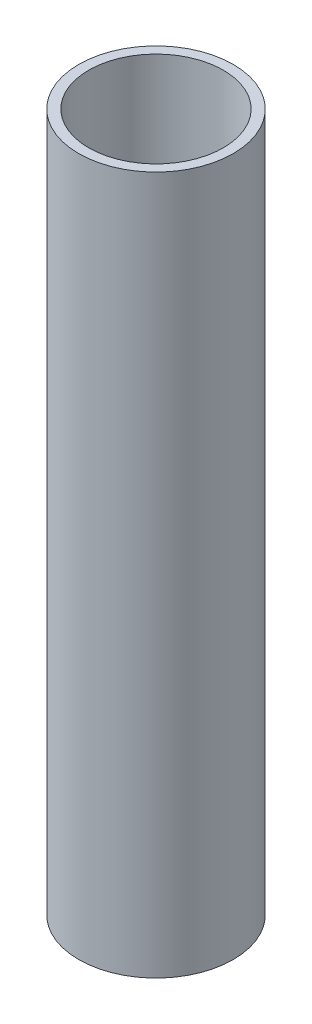
SolidWorks part; units mm, degrees
ref_plane "Front Plane" through (0, 0, 0) normal (0, 0, 1) x (1, 0, 0)
ref_plane "Top Plane" through (0, 0, 0) normal (0, 1, 0) x (1, 0, 0)
ref_plane "Right Plane" through (0, 0, 0) normal (1, 0, 0) x (0, 0, -1)
sketch "Sketch1" plane through (0, 0, 0) normal (0, 1, 0) x (1, 0, 0)
  circle A0 centre (0, 0) radius 15.5
  circle A1 centre (0, 0) radius 13.5
  dimension "D1" = 31
  dimension "D2" = 2
extrude "Boss-Extrude1" add sketch "Sketch1" along normal blind 140
